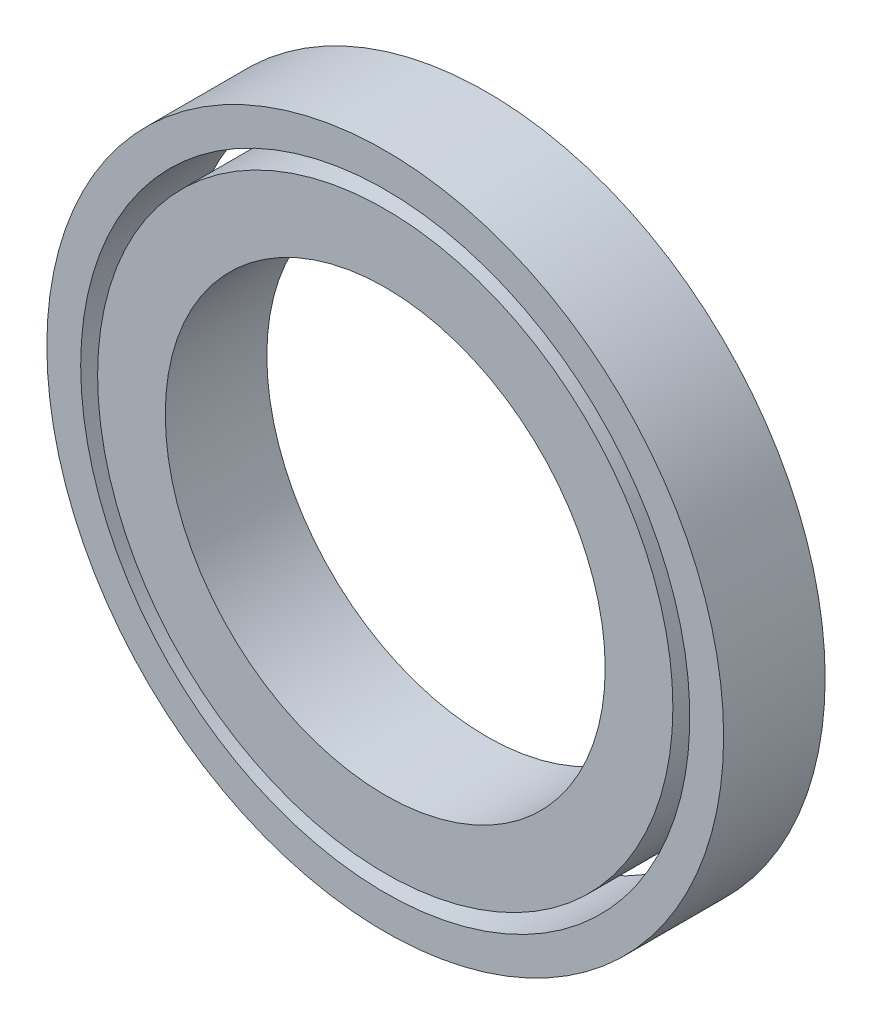
SolidWorks part; units mm, degrees
ref_plane "Front Plane" through (0, 0, 0) normal (0, 0, 1) x (1, 0, 0)
ref_plane "Top Plane" through (0, 0, 0) normal (0, 1, 0) x (1, 0, 0)
ref_plane "Right Plane" through (0, 0, 0) normal (1, 0, 0) x (0, 0, -1)
sketch "Sketch1" plane through (0, 0, 0) normal (0, 0, 1) x (1, 0, 0)
  circle A0 centre (0, 0) radius 17
  circle A1 centre (0, 0) radius 13
extrude "Boss-Extrude1" add sketch "Sketch1" along normal blind 6
sketch "Sketch2" plane through (0, 0, 0) normal (0, 0, -1) x (-1, 0, 0)
  circle A0 centre (0, 0) radius 20
  circle A1 centre (0, 0) radius 18
extrude "Boss-Extrude2" add sketch "Sketch2" against normal blind 6 separate body
